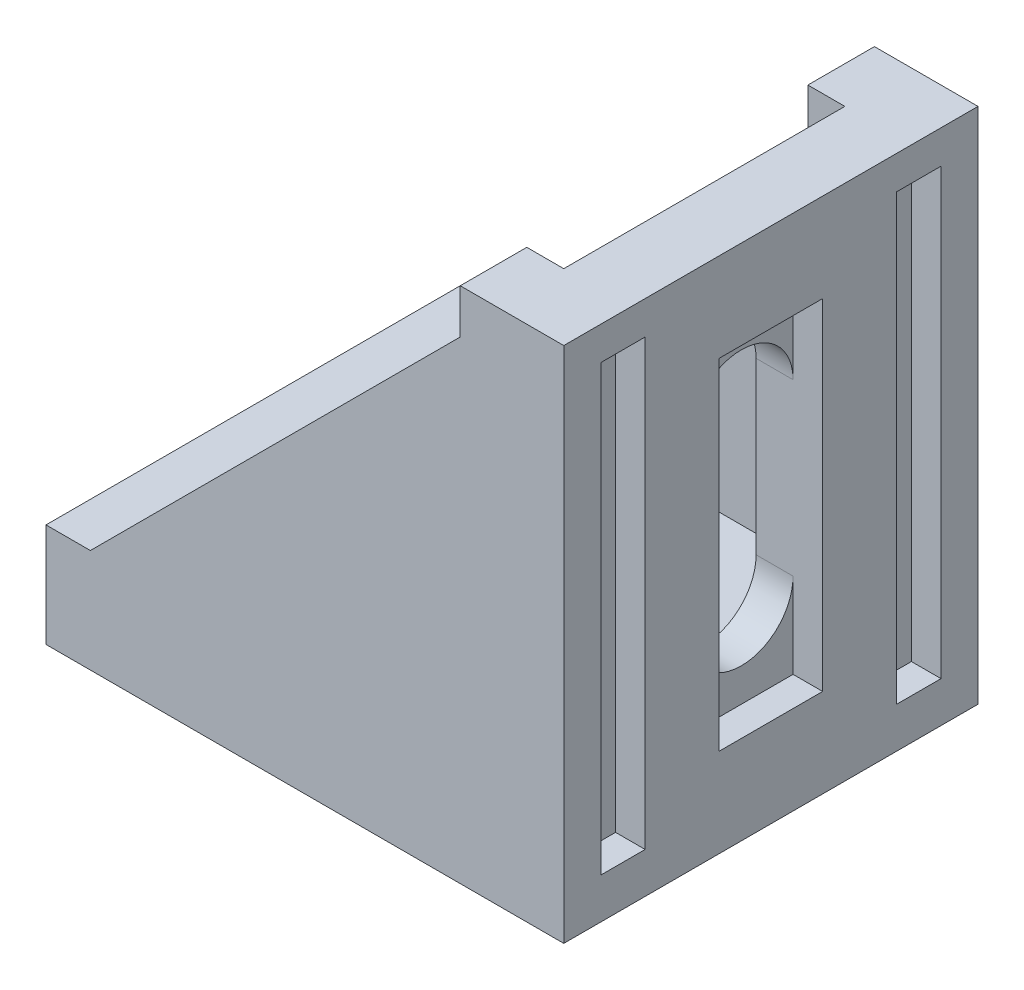
SolidWorks part; units mm, degrees
ref_plane "Front Plane" through (0, 0, 0) normal (0, 0, 1) x (1, 0, 0)
ref_plane "Top Plane" through (0, 0, 0) normal (0, 1, 0) x (1, 0, 0)
ref_plane "Right Plane" through (0, 0, 0) normal (1, 0, 0) x (0, 0, -1)
sketch "Sketch1" plane through (0, 0, 0) normal (0, 0, 1) x (1, 0, 0)
  line L0 (0, 0) -> (35, 0)
  line L1 (35, 0) -> (35, 35)
  line L2 (35, 35) -> (28, 35)
  line L3 (28, 35) -> (28, 32)
  line L4 (28, 32) -> (3, 7)
  line L5 (3, 7) -> (0, 7)
  line L6 (0, 7) -> (0, 0)
  point P8 (28, 32)
  dimension "D1" = 35
  dimension "D2" = 7
  dimension "D3" = 35
  dimension "D4" = 3
  dimension "D5" = 3
  dimension "D6" = 7
extrude "Boss-Extrude1" add sketch "Sketch1" along normal blind 28
sketch "Sketch3" plane through (0, 0, 0) normal (-1, 0, 0) x (0, 0, 1)
  line L0 (14, 59.391) -> (14, 10.609) construction
  line L5 (28, 35) -> (0, 35) construction
  line L6 (4.5, 35) -> (23.5, 35)
  line L7 (4.5, 35) -> (4.5, 7)
  line L8 (4.5, 7) -> (23.5, 7)
  line L9 (23.5, 35) -> (23.5, 7)
  line L10 (28, 7) -> (0, 7) construction
  point P7 (14, 35)
  dimension "D1" = 14
  dimension "D2" = 19
extrude "Cut-Extrude1" cut sketch "Sketch3" against normal blind 30.5
sketch "Sketch4" plane through (35, 0, 0) normal (1, 0, 0) x (0, 0, -1)
  line L0 (-14, 36.2436) -> (-14, -2.7537) construction
  line L1 (0, 0) -> (0, 35) construction
  line L2 (-28, 0) -> (-28, 35) construction
  line L3 (-25.5, 32.75) -> (-22.5, 32.75)
  line L4 (-25.5, 32.75) -> (-25.5, 2.75)
  line L5 (-25.5, 2.75) -> (-22.5, 2.75)
  line L6 (-22.5, 32.75) -> (-22.5, 2.75)
  line L7 (-28, 35) -> (0, 35) construction
  line L8 (-28, 0) -> (0, 0) construction
  line L9 (-2.5, 2.75) -> (-5.5, 2.75)
  line L10 (-2.5, 32.75) -> (-5.5, 32.75)
  line L11 (-2.5, 32.75) -> (-2.5, 2.75)
  line L12 (-5.5, 32.75) -> (-5.5, 2.75)
  dimension "D1" = 14
  dimension "D2" = 2.5
  dimension "D3" = 3
  dimension "D4" = 2.25
  dimension "D5" = 2.75
extrude "Cut-Extrude2" cut sketch "Sketch4" against normal blind 2
sketch "Sketch5" plane through (35, 0, 0) normal (1, 0, 0) x (0, 0, -1)
  line L0 (-14, 27.921) -> (-14, 10.114) construction
  line L1 (0, 0) -> (0, 35) construction
  line L2 (-14, 23.25) -> (-14, 11.75) construction
  line L3 (-10.5, 23.25) -> (-10.5, 11.75)
  line L4 (-17.5, 23.25) -> (-17.5, 11.75)
  line L5 (-28, 35) -> (0, 35) construction
  arc A0 (-10.5, 23.25) -> (-17.5, 23.25) centre (-14, 23.25) ccw
  arc A1 (-17.5, 11.75) -> (-10.5, 11.75) centre (-14, 11.75) ccw
  point P6 (-14, 17.5)
  dimension "D3" = 3.5
  dimension "D1" = 14
  dimension "D2" = 11.5
  dimension "D4" = 17.5
extrude "Cut-Extrude3" cut sketch "Sketch5" against normal through all
sketch "Sketch6" plane through (35, 0, 0) normal (1, 0, 0) x (0, 0, -1)
  line L0 (-14, 52.1845) -> (-14, 5.8155) construction
  line L1 (0, 0) -> (0, 35) construction
  line L2 (-28, 35) -> (0, 35) construction
  line L3 (-17.5, 29) -> (-10.5, 29)
  line L4 (-17.5, 29) -> (-17.5, 6)
  line L5 (-17.5, 6) -> (-10.5, 6)
  line L6 (-10.5, 29) -> (-10.5, 6)
  point P8 (-14, 29)
  point P9 (-10.5, 17.5)
  dimension "D1" = 14
  dimension "D2" = 23
  dimension "D3" = 7
  dimension "D4" = 17.5
extrude "Cut-Extrude4" cut sketch "Sketch6" against normal blind 2
sketch "Sketch7" plane through (35, 0, 0) normal (1, 0, 0) x (0, 0, -1)
  line L0 (-17, 29) -> (-11, 29)
  line L1 (-10.5, 29) -> (-17.5, 29) construction
  line L3 (-17.5, 29) -> (-17.5, 6) construction
  line L6 (-17, 29) -> (-17, 31)
  line L7 (-17, 31) -> (-11, 31)
  line L8 (-11, 31) -> (-11, 29)
  dimension "D1" = 6
  dimension "D2" = 0.5
  dimension "D5" = 2
extrude "Boss-Extrude2" [suppressed] add sketch "Sketch7" along normal blind 5
sketch "Sketch8" [suppressed] plane through (0, 0, 17) normal (0, 0, 1) x (1, 0, 0)
  line L0 (35, 31) -> (37, 29)
  line L5 (35, 31) -> (40, 31)
  line L6 (40, 31) -> (40, 29)
  line L7 (40, 29) -> (37, 29)
  point P10 (40.0869, 31)
  dimension "D1" = 45
  dimension "D2" = 5
  dimension "D3" = 3
extrude "Cut-Extrude5" [suppressed] cut sketch "Sketch8" against normal through all
fillet "Fillet1" [suppressed] radius 0.25
sketch "Sketch11" plane through (0, 0, 0) normal (0, -1, 0) x (1, 0, 0)
  line L4 (-5.0806, 14) -> (63.0806, 14) construction
  line L5 (0, 0) -> (35, 0) construction
  line L6 (0, 28) -> (0, 0) construction
  line L7 (2.5, 22.5) -> (32.25, 22.5)
  line L8 (2.5, 22.5) -> (2.5, 25.5)
  line L9 (2.5, 25.5) -> (32.25, 25.5)
  line L10 (32.25, 22.5) -> (32.25, 25.5)
  line L11 (35, 28) -> (35, 0) construction
  line L12 (0, 28) -> (35, 28) construction
  line L13 (2.5, 5.5) -> (2.5, 2.5)
  line L14 (2.5, 5.5) -> (32.25, 5.5)
  line L15 (32.25, 5.5) -> (32.25, 2.5)
  line L16 (2.5, 2.5) -> (32.25, 2.5)
  line L18 (29, 17.5) -> (6, 17.5)
  line L19 (29, 17.5) -> (29, 10.5)
  line L20 (29, 10.5) -> (6, 10.5)
  line L21 (6, 17.5) -> (6, 10.5)
  point P8 (2.5, 24)
  point P23 (17.5, 10.5)
  point P24 (29, 14)
  dimension "D1" = 14
  dimension "D2" = 3
  dimension "D3" = 2.5
  dimension "D4" = 2.75
  dimension "D5" = 2.5
  dimension "D6" = 23
  dimension "D7" = 7
  dimension "D8" = 17.5
extrude "Cut-Extrude6" cut sketch "Sketch11" against normal blind 2
sketch "Sketch12" plane through (0, 2, 0) normal (0, -1, 0) x (1, 0, 0)
  line L0 (7.5156, 14) -> (26.7738, 14) construction
  line L1 (0, 28) -> (35, 28) construction
  line L2 (11.75, 14) -> (23.25, 14) construction
  line L3 (11.75, 17.5) -> (23.25, 17.5)
  line L4 (11.75, 10.5) -> (23.25, 10.5)
  line L5 (0, 28) -> (0, 0) construction
  arc A0 (11.75, 17.5) -> (11.75, 10.5) centre (11.75, 14) ccw
  arc A1 (23.25, 10.5) -> (23.25, 17.5) centre (23.25, 14) ccw
  point P6 (17.5, 14)
  point P11 (15.2608, 14)
  dimension "D3" = 3.5
  dimension "D1" = 14
  dimension "D2" = 11.5
  dimension "D4" = 17.5
extrude "Cut-Extrude7" cut sketch "Sketch12" against normal through all
